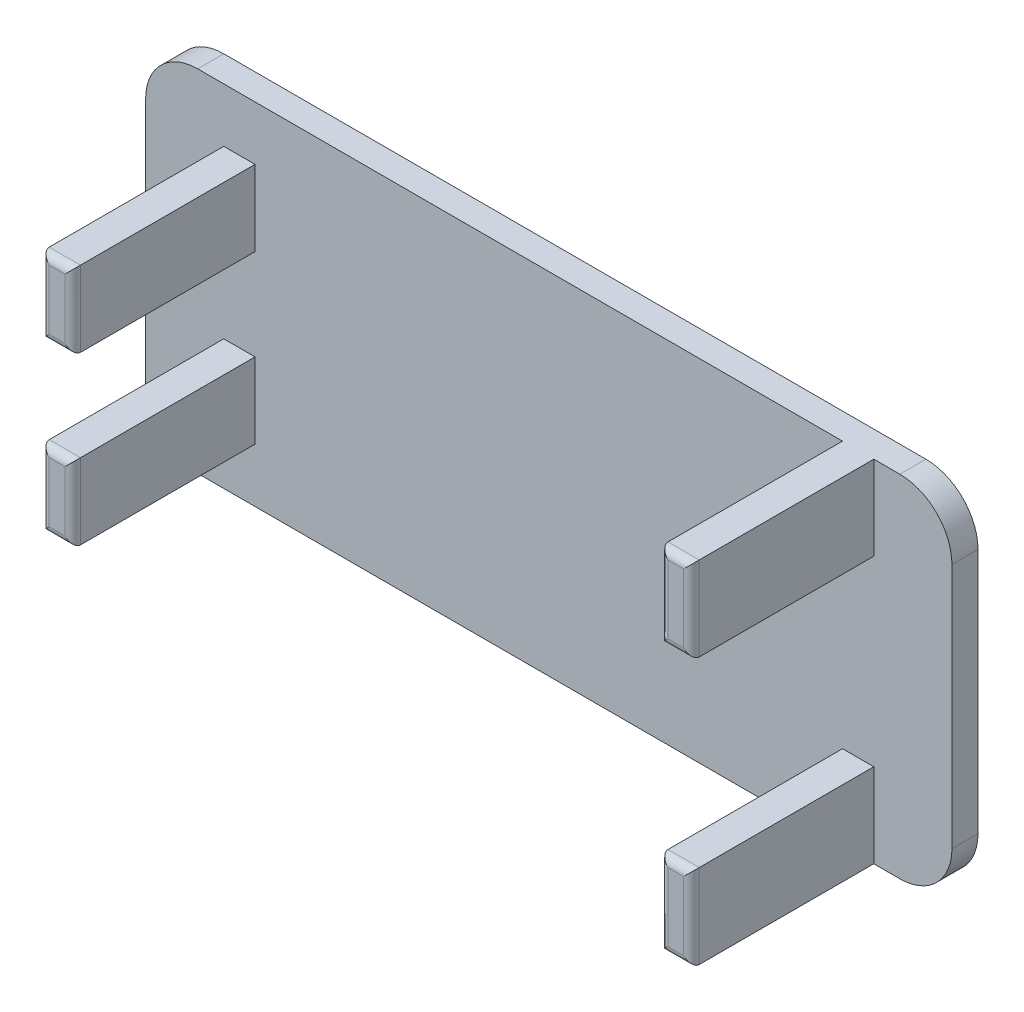
SolidWorks part; units mm, degrees
ref_plane "Front" through (0, 0, 0) normal (0, 0, 1) x (1, 0, 0)
ref_plane "Top" through (0, 0, 0) normal (0, 1, 0) x (1, 0, 0)
ref_plane "Right" through (0, 0, 0) normal (1, 0, 0) x (0, 0, -1)
sketch "草图1" plane through (0, 0, 0) normal (0, 0, 1) x (1, 0, 0)
  line L1 (2, 0) -> (28.95, 0)
  line L2 (0, 2) -> (0, 11.45)
  line L3 (2, 13.45) -> (28.95, 13.45)
  line L4 (30.95, 2) -> (30.95, 11.45)
  arc A0 (0, 11.45) -> (2, 13.45) centre (2, 11.45) cw
  arc A1 (28.95, 13.45) -> (30.95, 11.45) centre (28.95, 11.45) cw
  arc A2 (28.95, 0) -> (30.95, 2) centre (28.95, 2) ccw
  arc A3 (2, 0) -> (0, 2) centre (2, 2) cw
  point P7 (0, 13.45)
  point P12 (30.95, 0)
  point P15 (0, 0)
  dimension "D3" = 2
  dimension "D1" = 30.95
  dimension "D2" = 13.45
extrude "凸台-拉伸1" add sketch "草图1" along normal blind 1
sketch "草图2" plane through (0, 0, 1) normal (0, 0, 1) x (1, 0, 0)
  line L0 (28.95, 13.45) -> (2, 13.45) construction
  line L1 (26.75, 13.45) -> (27.95, 13.45)
  line L2 (26.75, 13.45) -> (26.75, 0)
  line L3 (26.75, 0) -> (27.95, 0)
  line L4 (27.95, 13.45) -> (27.95, 0)
  line L5 (2, 0) -> (28.95, 0) construction
  line L6 (30.95, 2) -> (30.95, 11.45) construction
  line L7 (3, 11.375) -> (4.2, 11.375)
  line L8 (3, 11.375) -> (3, 2.075)
  line L9 (3, 2.075) -> (4.2, 2.075)
  line L10 (4.2, 11.375) -> (4.2, 2.075)
  line L11 (0, 11.45) -> (0, 2) construction
  point P16 (3, 6.725)
  point P17 (0, 6.725)
  dimension "D1" = 3
  dimension "D2" = 1.2
  dimension "D3" = 1.2
  dimension "D4" = 3
  dimension "D5" = 0
  dimension "D6" = 9.3
extrude "凸台-拉伸2" add sketch "草图2" along normal blind 7
sketch "草图3" plane through (27.95, 0, 0) normal (1, 0, 0) x (0, 0, -1)
  line L0 (-8, 0) -> (-8, 13.45) construction
  line L1 (-8, 10.225) -> (-1, 10.225)
  line L2 (-8, 10.225) -> (-8, 3.225)
  line L3 (-8, 3.225) -> (-1, 3.225)
  line L4 (-1, 10.225) -> (-1, 3.225)
  line L5 (-1, 0) -> (-1, 13.45) construction
  point P6 (-1, 6.725)
  point P9 (-1, 6.725)
  dimension "D1" = 0
  dimension "D2" = 7
  dimension "D3" = 7
extrude "切除-拉伸1" cut sketch "草图3" against normal up to next
sketch "草图4" plane through (3, 0, 0) normal (-1, 0, 0) x (0, 0, 1)
  line L0 (8, 11.375) -> (8, 2.075) construction
  line L1 (8, 4.975) -> (1, 4.975)
  line L2 (8, 4.975) -> (8, 8.475)
  line L3 (8, 8.475) -> (1, 8.475)
  line L4 (1, 4.975) -> (1, 8.475)
  line L5 (1, 11.375) -> (1, 2.075) construction
  point P8 (8, 6.725)
  point P9 (8, 6.725)
  dimension "D1" = 0
  dimension "D2" = 3.5
extrude "切除-拉伸2" cut sketch "草图4" against normal up to next
fillet "圆角1" radius 0.3 16 edges at (27.95, 1.6125, 8) (27.35, 0, 8) (26.75, 1.6125, 8) (26.75, 11.8375, 8) (27.35, 13.45, 8) (27.95, 11.8375, 8) (4.2, 3.525, 8) (3, 3.525, 8) (3, 9.925, 8) (4.2, 9.925, 8) (3.6, 11.375, 8) (3.6, 4.975, 8) (3.6, 2.075, 8) (3.6, 8.475, 8) (27.35, 3.225, 8) (27.35, 10.225, 8)
